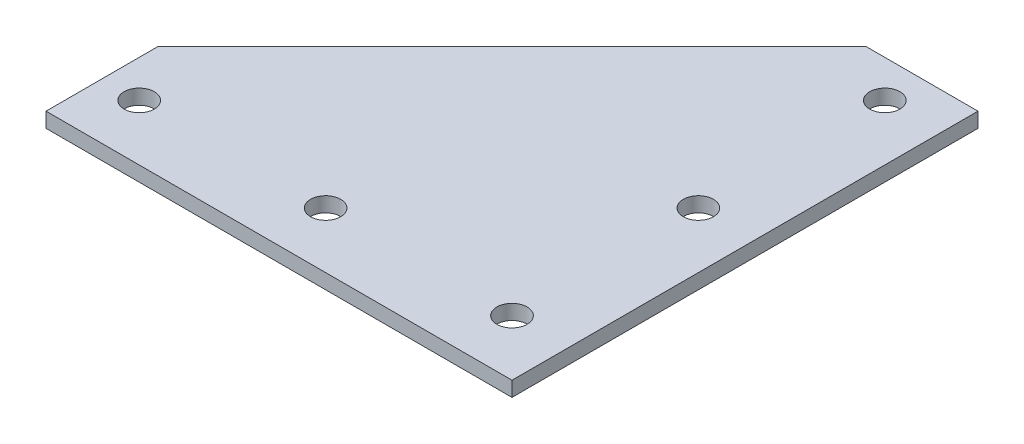
SolidWorks part; units mm, degrees
material "6061-T6 (SS)"
ref_plane "Front Plane" through (0, 0, 0) normal (0, 0, 1) x (1, 0, 0)
ref_plane "Top Plane" through (0, 0, 0) normal (0, 1, 0) x (1, 0, 0)
ref_plane "Right Plane" through (0, 0, 0) normal (1, 0, 0) x (0, 0, -1)
sketch "Sketch1" plane through (0, 0, 0) normal (0, 1, 0) x (1, 0, 0)
  line L0 (0, 0) -> (-100, 0) construction
  line L1 (0, 0) -> (0, 100) construction
  line L2 (15, -15) -> (-110, -15)
  line L3 (15, -15) -> (15, 110)
  line L4 (-110, -15) -> (-110, 15)
  line L5 (-110, 15) -> (-15, 110)
  line L6 (-15, 110) -> (15, 110)
  circle A0 centre (-100, 0) radius 4.05
  circle A1 centre (-50, 0) radius 4.05
  circle A2 centre (0, 0) radius 4.05
  circle A3 centre (0, 100) radius 4.05
  circle A4 centre (0, 50) radius 4.05
  dimension "D1" = 8.1
  dimension "D2" = 100
  dimension "D3" = 15
  dimension "D4" = 15
  dimension "D5" = 30
  dimension "D6" = 10
extrude "Boss-Extrude1" add sketch "Sketch1" along normal blind 4
